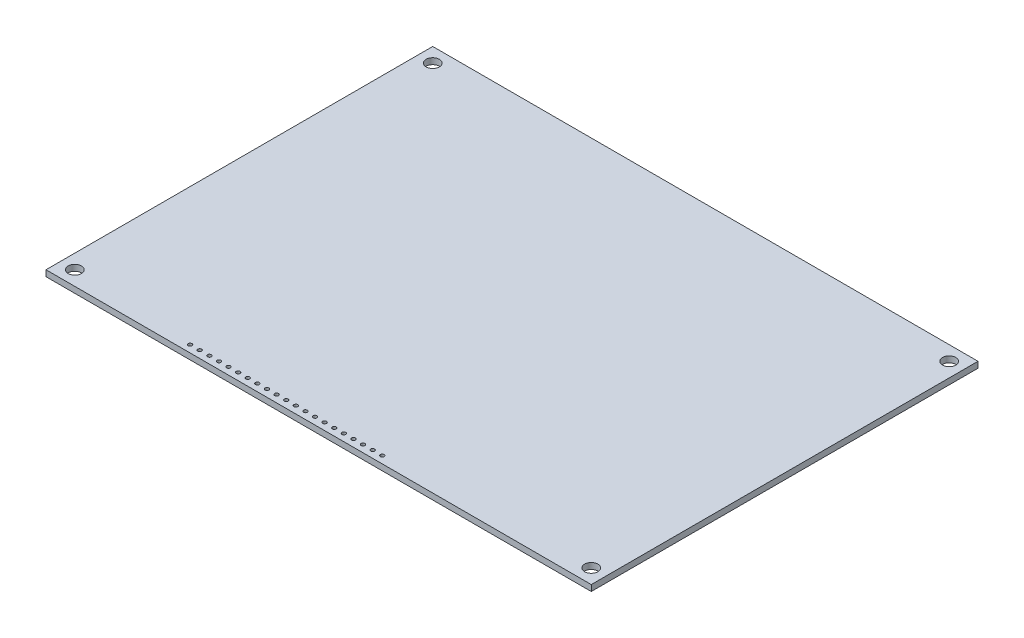
SolidWorks part; units mm, degrees
ref_plane "Front Plane" through (0, 0, 0) normal (0, 0, 1) x (1, 0, 0)
ref_plane "Top Plane" through (0, 0, 0) normal (0, 1, 0) x (1, 0, 0)
ref_plane "Right Plane" through (0, 0, 0) normal (1, 0, 0) x (0, 0, -1)
sketch "Sketch1" plane through (0, 0, 0) normal (0, 1, 0) x (1, 0, 0)
  line L1 (0, 0) -> (144.145, 0)
  line L2 (0, 0) -> (0, 102.235)
  line L3 (0, 102.235) -> (144.145, 102.235)
  line L4 (144.145, 0) -> (144.145, 102.235)
  circle A0 centre (3.815, 98.42) radius 1.7526
  circle A1 centre (140.33, 98.42) radius 1.7526
  circle A2 centre (140.33, 3.815) radius 1.7526
  circle A3 centre (3.815, 3.815) radius 1.7526
  dimension "D3" = 3.5052
  dimension "D1" = 144.145
  dimension "D2" = 102.235
  dimension "D4" = 3.815
  dimension "D5" = 3.815
  dimension "D6" = 3.815
  dimension "D7" = 3.815
extrude "Boss-Extrude1" add sketch "Sketch1" along normal blind 1.6
sketch "Sketch2" plane through (0, 1.6, 0) normal (0, 1, 0) x (1, 0, 0)
  line L0 (0, 0) -> (144.145, 0) construction
  circle A0 centre (36.2, 1.9) radius 0.5
  circle A1 centre (3.815, 3.815) radius 1.7526 construction
  circle A2 centre (38.74, 1.9) radius 0.5
  circle A3 centre (41.28, 1.9) radius 0.5
  circle A4 centre (43.82, 1.9) radius 0.5
  circle A5 centre (46.36, 1.9) radius 0.5
  circle A6 centre (48.9, 1.9) radius 0.5
  circle A7 centre (51.44, 1.9) radius 0.5
  circle A8 centre (53.98, 1.9) radius 0.5
  circle A9 centre (56.52, 1.9) radius 0.5
  circle A10 centre (59.06, 1.9) radius 0.5
  circle A11 centre (61.6, 1.9) radius 0.5
  circle A12 centre (64.14, 1.9) radius 0.5
  circle A13 centre (66.68, 1.9) radius 0.5
  circle A14 centre (69.22, 1.9) radius 0.5
  circle A15 centre (71.76, 1.9) radius 0.5
  circle A16 centre (74.3, 1.9) radius 0.5
  circle A17 centre (76.84, 1.9) radius 0.5
  circle A18 centre (79.38, 1.9) radius 0.5
  circle A19 centre (81.92, 1.9) radius 0.5
  circle A20 centre (84.46, 1.9) radius 0.5
  circle A21 centre (87, 1.9) radius 0.5
  point P7 (38.7415, 1.9)
  dimension "D3" = 1
  dimension "D1" = 32.385
  dimension "D2" = 1.9
  dimension "D5" = 2.54
  dimension "D4" = 21
extrude "Cut-Extrude1" cut sketch "Sketch2" against normal through all
